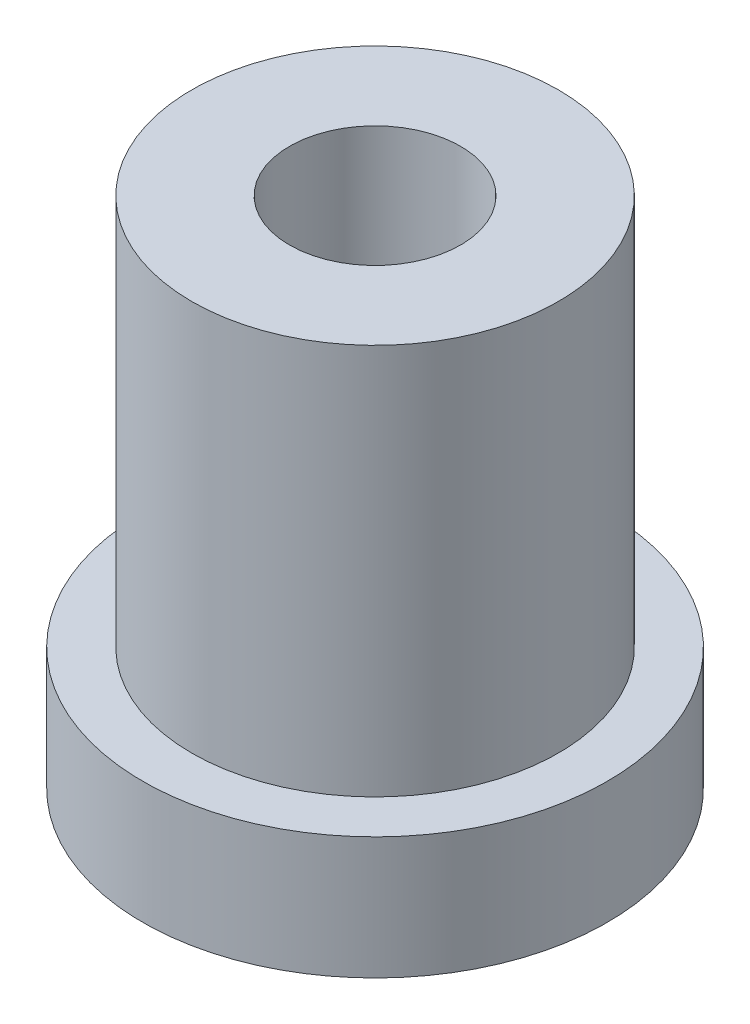
SolidWorks part; units mm, degrees
ref_plane "Front Plane" through (0, 0, 0) normal (0, 0, 1) x (1, 0, 0)
ref_plane "Top Plane" through (0, 0, 0) normal (0, 1, 0) x (1, 0, 0)
ref_plane "Right Plane" through (0, 0, 0) normal (1, 0, 0) x (0, 0, -1)
sketch "Sketch1" plane through (0, 0, 0) normal (0, 1, 0) x (1, 0, 0)
  circle A0 centre (0, 0) radius 3.75
  dimension "D1" = 7.5
extrude "Boss-Extrude1" add sketch "Sketch1" along normal blind 10.5
hole_wizard "Ø3.5 (3.5) Diameter Hole1" positions "Sketch4" profile "Sketch3" hole size "Ø3.5" standard "JIS" end condition through all
sketch "Sketch4" plane through (0, 10.5, 0) normal (0, 1, 0) x (1, 0, 0)
  point P0 (0, 0)
sketch "Sketch3" plane through (0, 10.5, 0) normal (1, 0, 0) x (0, 0, 1)
  line L0 (0, 0) -> (0, 10.5)
  line L1 (0, 10.5) -> (1.75, 10.5)
  line L2 (1.75, 10.5) -> (1.75, 0)
  line L5 (1.75, 0) -> (0, 0)
  line L11 (0, -6.35) -> (0, 107.95) construction
  dimension "Thru Hole Dia." = 3.5
  dimension "Thru Hole Depth" = 10.5
sketch "Sketch5" plane through (0, 0, 0) normal (0, -1, 0) x (1, 0, 0)
  circle A0 centre (0, 0) radius 3.75 construction
  circle A1 centre (0, 0) radius 3.75
  circle A2 centre (0, 0) radius 4.75
  dimension "D1" = 9.5
extrude "Boss-Extrude2" add sketch "Sketch5" against normal blind 2.5
